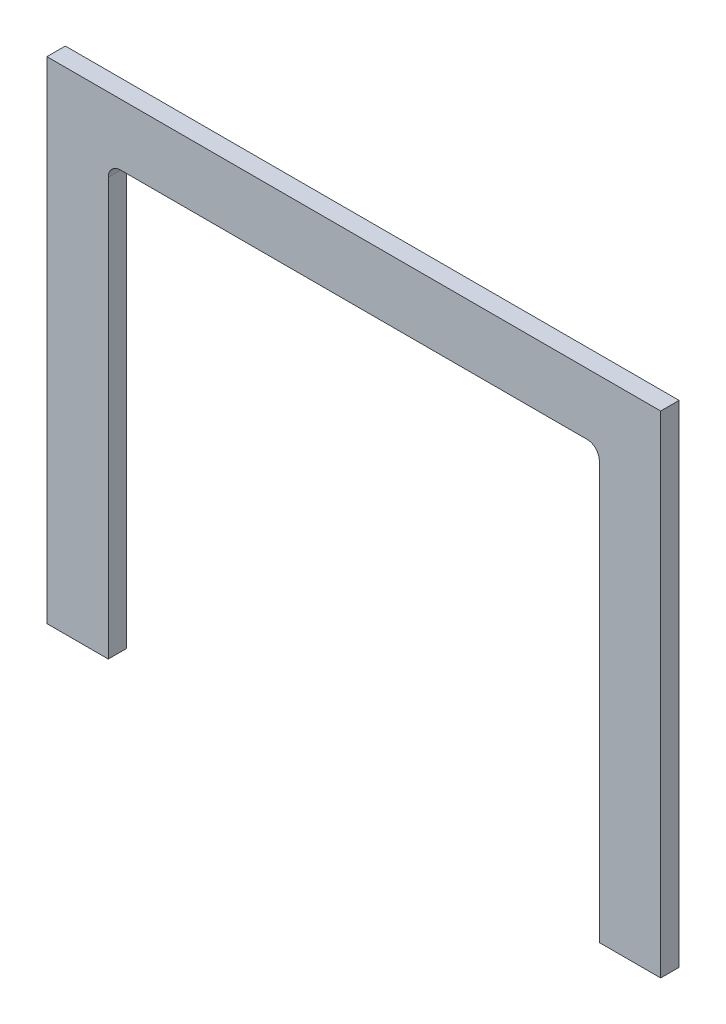
SolidWorks part; units mm, degrees
material "Beech"
ref_plane "Plan de face" through (0, 0, 0) normal (0, 0, 1) x (1, 0, 0)
ref_plane "Plan de dessus" through (0, 0, 0) normal (0, 1, 0) x (1, 0, 0)
ref_plane "Plan de droite" through (0, 0, 0) normal (1, 0, 0) x (0, 0, -1)
sketch "Sketch1" plane through (0, 0, 0) normal (0, 0, 1) x (1, 0, 0)
  line L0 (-250, -200) -> (-200, -200)
  line L2 (-250, -200) -> (-250, 200)
  line L3 (-250, 200) -> (250, 200)
  line L4 (250, -200) -> (250, 200)
  line L5 (-250, -200) -> (250, 200) construction
  line L6 (-250, 200) -> (250, -200) construction
  line L7 (-200, -200) -> (-200, 140)
  line L8 (-190, 150) -> (190, 150)
  line L9 (200, 140) -> (200, -200)
  line L10 (200, -200) -> (250, -200)
  arc A0 (200, 140) -> (190, 150) centre (190, 140) ccw
  arc A1 (-190, 150) -> (-200, 140) centre (-190, 140) ccw
  point P0 (0, 0)
  dimension "D3" = 10
  dimension "D1" = 400
  dimension "D2" = 400
  dimension "D4" = 50
  dimension "D5" = 50
  dimension "D6" = 50
  dimension "D7" = 400
extrude "Boss-Extrude1" add sketch "Sketch1" along normal blind 15
